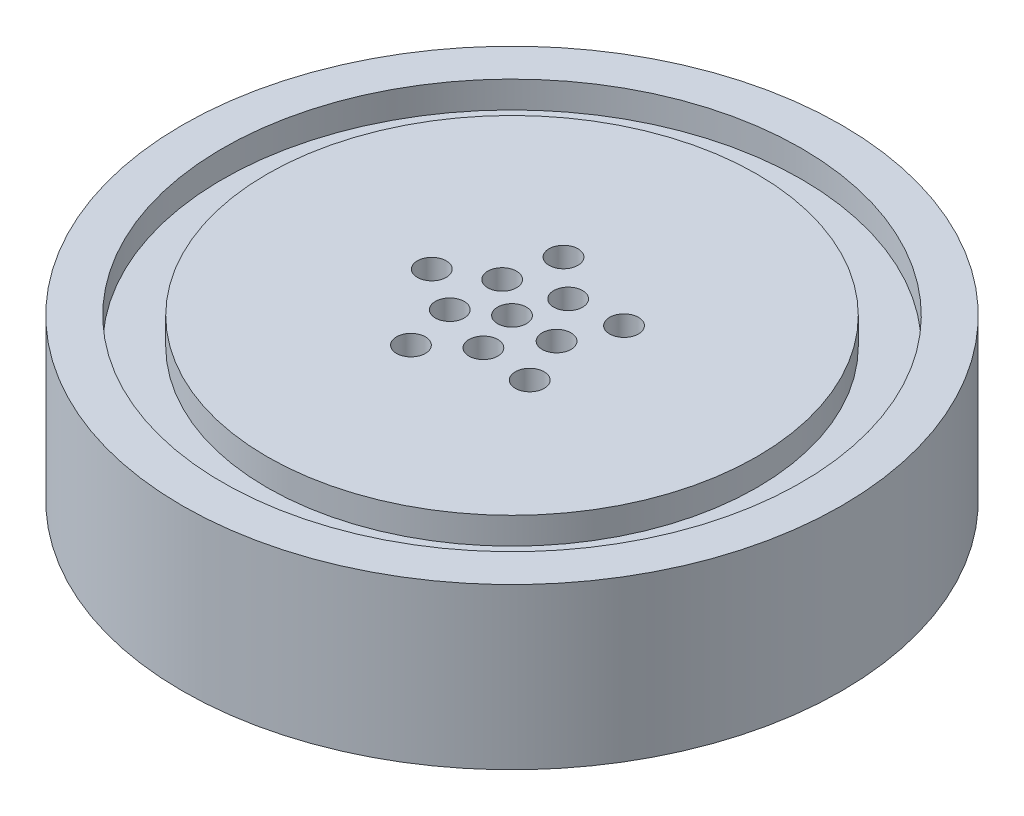
SolidWorks part; units mm, degrees
material "6061-T6 (SS)"
ref_plane "Front Plane" through (0, 0, 0) normal (0, 0, 1) x (1, 0, 0)
ref_plane "Top Plane" through (0, 0, 0) normal (0, 1, 0) x (1, 0, 0)
ref_plane "Right Plane" through (0, 0, 0) normal (1, 0, 0) x (0, 0, -1)
ref_axis "Axis1" through (0, -0.4763, 0) along (0, 1, 0)
sketch "Sketch2" plane through (0, 0, 0) normal (0, 1, 0) x (1, 0, 0)
  circle A0 centre (0, 0) radius 23.495
  dimension "D1" = 46.99
extrude "Boss-Extrude1" add sketch "Sketch2" along normal blind 11.43
ref_plane "Plane1" through (0, 11.43, 0) normal (0, 1, 0) x (1, 0, 0)
sketch "Sketch8" plane through (0, 0, 0) normal (0, 0, 1) x (1, 0, 0)
  line L0 (27.94, 11.43) -> (-27.94, 11.43) construction
  line L1 (17.4498, 11.43) -> (20.6248, 11.43)
  line L2 (17.4498, 11.43) -> (17.4498, 9.525)
  line L3 (17.4498, 9.525) -> (20.6248, 9.525)
  line L4 (20.6248, 11.43) -> (20.6248, 9.525)
  line L6 (0, -0.4763) -> (0, 10.0012) construction
  dimension "D1" = 20.6248
  dimension "D2" = 3.175
  dimension "D3" = 1.905
revolve "Cut-Revolve1" cut sketch "Sketch8" angle 360 about axis through (0, -0.4763, 0) along (0, 1, 0)
sketch "Sketch12" plane through (0, 0, 0) normal (0, -1, 0) x (1, 0, 0)
  circle A0 centre (0, 0) radius 9.525
  dimension "D1" = 19.05
extrude "Boss-Extrude2" add sketch "Sketch12" along normal blind 6.35
hole_wizard "#46 (0.081) Diameter Hole1" positions "Sketch3" profile "Sketch4" hole size "#46" standard "ANSI Inch" end condition up to next
sketch "Sketch3" plane through (0, 11.43, 0) normal (0, 1, 0) x (1, 0, 0)
  line L0 (-9.779, 0) -> (9.779, 0) construction
  line L1 (4.9318, -3.5831) -> (0, 0) construction
  line L2 (-6.096, 0) -> (0, 0) construction
  point P0 (-5.715, 0)
  point P12 (-2.5686, 1.8662)
  point P16 (0, 0)
  point P23 (-1.766, 5.4353)
  point P24 (4.6235, 3.3592)
  point P25 (4.6235, -3.3592)
  point P26 (-1.766, -5.4353)
  point P34 (0, 0)
  point P39 (0.9811, 3.0196)
  point P40 (3.175, 0)
  point P44 (0, 0)
  point P134 (0.9811, -3.0196)
  point P135 (-2.5686, -1.8662)
  point P136 (0, 0)
  dimension "D1" = 5.715
  dimension "D2" = 3.175
  dimension "D5" = 36
  dimension "D3" = 5
  dimension "D4" = 5
sketch "Sketch4" plane through (-5.715, 11.43, 0) normal (1, 0, 0) x (0, 0, 1)
  line L0 (0, 0) -> (0, 17.78)
  line L1 (0, 17.78) -> (1.0287, 17.78)
  line L2 (1.0287, 17.78) -> (1.0287, 0)
  line L5 (1.0287, 0) -> (0, 0)
  line L11 (0, -6.35) -> (0, 107.95) construction
  dimension "Thru Hole Dia." = 2.0574
  dimension "Thru Hole Depth" = 17.78
